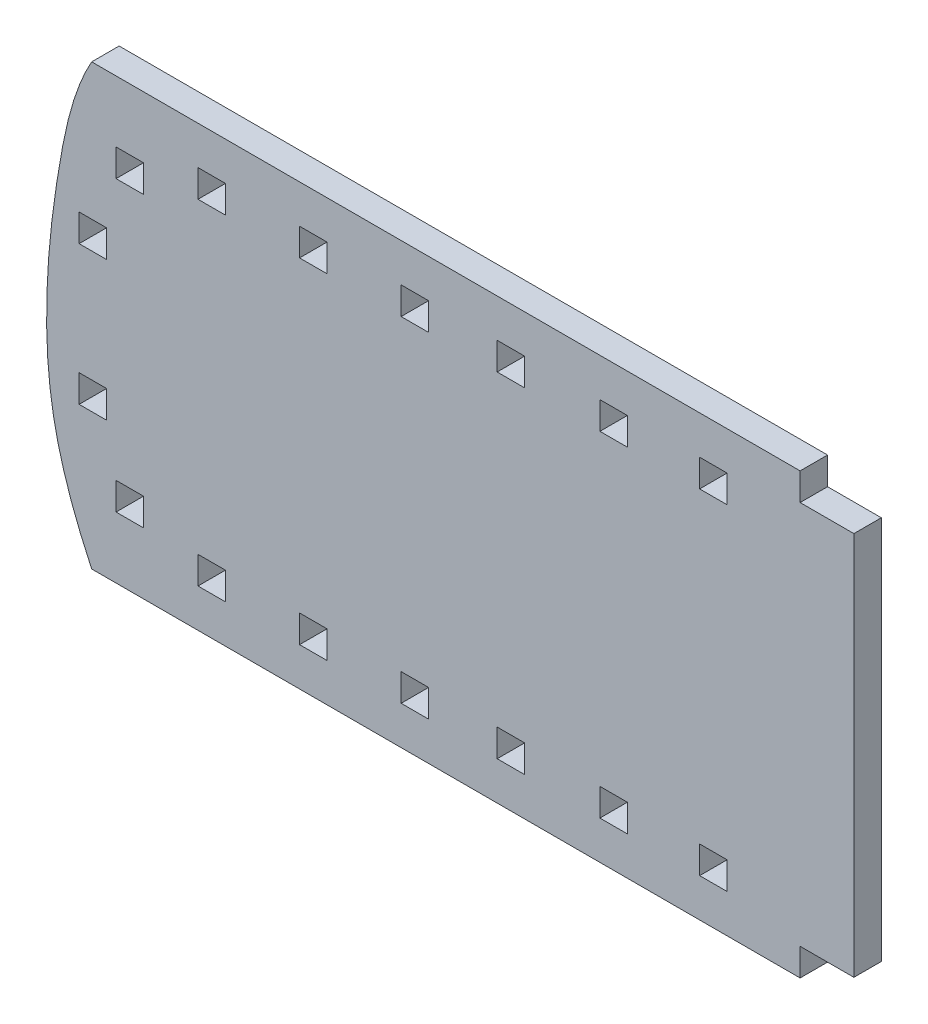
SolidWorks part; units mm, degrees
ref_plane "Front Plane" through (0, 0, 0) normal (0, 0, 1) x (1, 0, 0)
ref_plane "Top Plane" through (0, 0, 0) normal (0, 1, 0) x (1, 0, 0)
ref_plane "Right Plane" through (0, 0, 0) normal (1, 0, 0) x (0, 0, -1)
sketch "Sketch1" plane through (0, 0, 0) normal (0, 0, 1) x (1, 0, 0)
  line L0 (47.7382, 0) -> (129.678, 0)
  line L1 (129.678, 0) -> (129.678, -3.175)
  line L2 (47.7382, -3.175) -> (136.3694, -3.175) construction
  line L3 (129.678, -3.175) -> (145.4216, -3.175)
  line L4 (145.4216, -3.175) -> (145.4216, -47.625)
  line L5 (145.4216, -47.625) -> (129.678, -47.625)
  line L6 (129.678, -47.625) -> (129.678, -51.489)
  line L7 (129.678, -51.489) -> (47.7382, -50.8)
  spline S0 degree 3 poles (47.7382, 0) (41.3931, -1.7111) (30.5304, -9.3675) (28.6814, -25.6228) (30.4013, -42.1318) (41.7219, -48.4932) (47.7382, -50.8) knots 0 0 0 0 0.298782 0.512669 0.698135 1 1 1 1
extrude "Boss-Extrude1" add sketch "Sketch1" along normal blind 3.175 contours S0 L7 L6 L5 L4 L3 L1 L0
sketch "Sketch2" plane through (0, 0, 3.175) normal (0, 0, 1) x (1, 0, 0)
  line L1 (47.7382, 0) -> (25.9442, 0)
  line L2 (25.9442, 0) -> (25.9442, -50.8)
  line L3 (25.9442, -50.8) -> (47.7382, -50.8)
  spline S0 degree 3 poles (47.7382, 0) (45.6815, -3.6472) (43.6451, -12.8877) (42.1761, -25.6996) (42.9817, -39.0481) (45.8027, -46.7252) (47.7382, -50.8) knots 0 0 0 0 0.238684 0.536925 0.740325 1 1 1 1
extrude "Cut-Extrude1" cut sketch "Sketch2" against normal blind 3.175
sketch "Sketch3" plane through (0, 0, 3.175) normal (0, 0, 1) x (1, 0, 0)
  line L0 (145.4216, -25.4) -> (42.573, -25.4)
  line L1 (46.285, -31.8606) -> (49.46, -31.8606)
  line L2 (46.285, -31.8606) -> (46.285, -35.0356)
  line L3 (46.285, -35.0356) -> (49.46, -35.0356)
  line L4 (49.46, -31.8606) -> (49.46, -35.0356)
  line L5 (50.5572, -40.5118) -> (53.7322, -40.5118)
  line L6 (50.5572, -40.5118) -> (50.5572, -43.6868)
  line L7 (50.5572, -43.6868) -> (53.7322, -43.6868)
  line L8 (53.7322, -40.5118) -> (53.7322, -43.6868)
  line L9 (60.0337, -43.182) -> (63.2087, -43.182)
  line L10 (60.0337, -43.182) -> (60.0337, -46.357)
  line L11 (60.0337, -46.357) -> (63.2087, -46.357)
  line L12 (63.2087, -43.182) -> (63.2087, -46.357)
  line L13 (71.7823, -43.182) -> (74.9573, -43.182)
  line L14 (71.7823, -43.182) -> (71.7823, -46.357)
  line L15 (71.7823, -46.357) -> (74.9573, -46.357)
  line L16 (74.9573, -43.182) -> (74.9573, -46.357)
  line L17 (83.5309, -43.182) -> (86.7059, -43.182)
  line L18 (83.5309, -43.182) -> (83.5309, -46.357)
  line L19 (83.5309, -46.357) -> (86.7059, -46.357)
  line L20 (86.7059, -43.182) -> (86.7059, -46.357)
  line L21 (94.6387, -43.182) -> (97.8137, -43.182)
  line L22 (94.6387, -43.182) -> (94.6387, -46.357)
  line L23 (94.6387, -46.357) -> (97.8137, -46.357)
  line L24 (97.8137, -43.182) -> (97.8137, -46.357)
  line L25 (106.5233, -43.182) -> (109.6983, -43.182)
  line L26 (106.5233, -43.182) -> (106.5233, -46.357)
  line L27 (106.5233, -46.357) -> (109.6983, -46.357)
  line L28 (109.6983, -43.182) -> (109.6983, -46.357)
  line L29 (118.0583, -43.182) -> (121.2333, -43.182)
  line L30 (118.0583, -43.182) -> (118.0583, -46.357)
  line L31 (118.0583, -46.357) -> (121.2333, -46.357)
  line L32 (121.2333, -43.182) -> (121.2333, -46.357)
  line L33 (145.4216, -3.175) -> (145.4216, -47.625) construction
  line L34 (121.2333, -7.618) -> (121.2333, -4.443)
  line L35 (118.0583, -4.443) -> (121.2333, -4.443)
  line L36 (118.0583, -7.618) -> (118.0583, -4.443)
  line L37 (118.0583, -7.618) -> (121.2333, -7.618)
  line L38 (109.6983, -7.618) -> (109.6983, -4.443)
  line L39 (106.5233, -4.443) -> (109.6983, -4.443)
  line L40 (106.5233, -7.618) -> (106.5233, -4.443)
  line L41 (106.5233, -7.618) -> (109.6983, -7.618)
  line L42 (97.8137, -7.618) -> (97.8137, -4.443)
  line L43 (94.6387, -4.443) -> (97.8137, -4.443)
  line L44 (94.6387, -7.618) -> (94.6387, -4.443)
  line L45 (94.6387, -7.618) -> (97.8137, -7.618)
  line L46 (86.7059, -7.618) -> (86.7059, -4.443)
  line L47 (83.5309, -4.443) -> (86.7059, -4.443)
  line L48 (83.5309, -7.618) -> (83.5309, -4.443)
  line L49 (83.5309, -7.618) -> (86.7059, -7.618)
  line L50 (74.9573, -7.618) -> (74.9573, -4.443)
  line L51 (71.7823, -4.443) -> (74.9573, -4.443)
  line L52 (71.7823, -7.618) -> (71.7823, -4.443)
  line L53 (71.7823, -7.618) -> (74.9573, -7.618)
  line L54 (63.2087, -7.618) -> (63.2087, -4.443)
  line L55 (60.0337, -4.443) -> (63.2087, -4.443)
  line L56 (60.0337, -7.618) -> (60.0337, -4.443)
  line L57 (60.0337, -7.618) -> (63.2087, -7.618)
  line L58 (53.7322, -10.2882) -> (53.7322, -7.1132)
  line L59 (50.5572, -7.1132) -> (53.7322, -7.1132)
  line L60 (50.5572, -10.2882) -> (50.5572, -7.1132)
  line L61 (50.5572, -10.2882) -> (53.7322, -10.2882)
  line L62 (49.46, -18.9394) -> (49.46, -15.7644)
  line L63 (46.285, -15.7644) -> (49.46, -15.7644)
  line L64 (46.285, -18.9394) -> (46.285, -15.7644)
  line L65 (46.285, -18.9394) -> (49.46, -18.9394)
  spline S0 degree 3 poles (47.7382, -50.8) (45.8027, -46.7252) (42.9817, -39.0481) (42.1761, -25.6996) (43.6451, -12.8877) (45.6815, -3.6472) (47.7382, 0) knots 0 0 0 0 0.259675 0.463075 0.761316 1 1 1 1 construction
  dimension "D1" = 3.175
  dimension "D2" = 3.175
extrude "Cut-Extrude2" cut sketch "Sketch3" against normal blind 3.175 contours L56 L57 L54 L55 | L52 L53 L50 L51 | L48 L49 L46 L47 | L44 L45 L42 L43 | L40 L41 L38 L39 | L36 L37 L34 L35 | L60 L61 L58 L59 | L64 L65 L62 L63 | L4 L1 L2 L3 | L8 L5 L6 L7 | L12 L9 L10 L11 | L16 L13 L14 L15 | L20 L17 L18 L19 | L24 L21 L22 L23 | L28 L25 L26 L27 | L32 L29 L30 L31
sketch "Sketch4" plane through (0, 0, 3.175) normal (0, 0, 1) x (1, 0, 0)
  line L0 (145.4216, -47.625) -> (129.678, -47.625) construction
  line L1 (145.4216, -3.175) -> (135.8966, -3.175)
  line L2 (145.4216, -3.175) -> (145.4216, -47.625)
  line L3 (145.4216, -47.625) -> (135.8966, -47.625)
  line L4 (135.8966, -3.175) -> (135.8966, -47.625)
  dimension "D1" = 9.525
extrude "Cut-Extrude3" cut sketch "Sketch4" against normal blind 3.175
sketch "Sketch5" plane through (0, 0, 3.175) normal (0, 0, 1) x (1, 0, 0)
  line L0 (47.7382, -50.8) -> (131.865, -50.8)
  line L1 (47.7382, -50.8) -> (136.3694, -50.8) construction
  line L2 (131.865, -50.8) -> (131.865, -55.4968)
  line L3 (131.865, -55.4968) -> (47.7382, -50.8)
  line L4 (47.7382, -50.8) -> (47.8121, -50.7333)
extrude "Cut-Extrude4" cut sketch "Sketch5" against normal blind 3.175 contours L3 L2 L0
